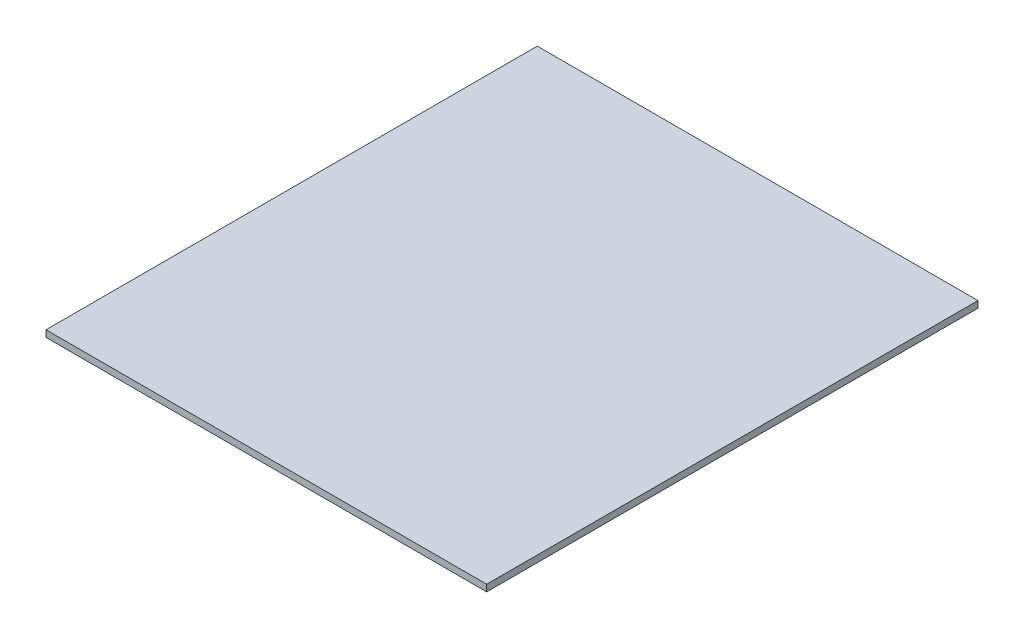
SolidWorks part; units mm, degrees
ref_plane "Front Plane" through (0, 0, 0) normal (0, 0, 1) x (1, 0, 0)
ref_plane "Top Plane" through (0, 0, 0) normal (0, 1, 0) x (1, 0, 0)
ref_plane "Right Plane" through (0, 0, 0) normal (1, 0, 0) x (0, 0, -1)
sketch "Sketch1" plane through (0, 0, 0) normal (0, 1, 0) x (1, 0, 0)
  line L1 (-331, -369) -> (331, -369)
  line L2 (-331, -369) -> (-331, 369)
  line L3 (-331, 369) -> (331, 369)
  line L4 (331, -369) -> (331, 369)
  line L5 (-331, -369) -> (331, 369) construction
  line L6 (-331, 369) -> (331, -369) construction
  point P0 (0, 0)
  dimension "D1" = 738
  dimension "D2" = 662
extrude "Boss-Extrude1" add sketch "Sketch1" against normal blind 10
